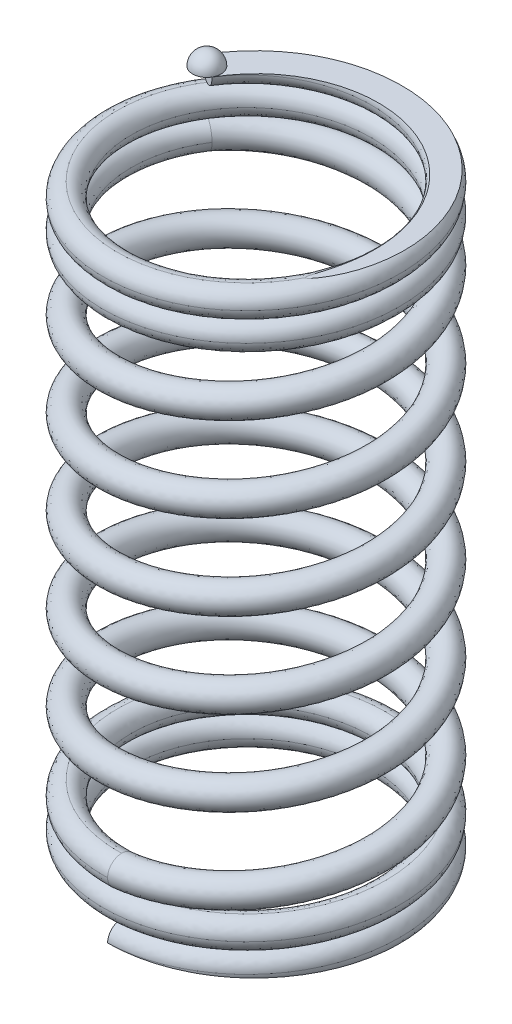
SolidWorks part; units mm, degrees
ref_plane "Front Plane" through (0, 0, 0) normal (0, 0, 1) x (1, 0, 0)
ref_plane "Top Plane" through (0, 0, 0) normal (0, 1, 0) x (1, 0, 0)
ref_plane "Right Plane" through (0, 0, 0) normal (1, 0, 0) x (0, 0, -1)
sketch "Sketch3" plane through (0, 0, 0) normal (0, 1, 0) x (1, 0, 0)
  circle A0 centre (0, 0) radius 4.75
  dimension "D1" = 9.5
ref_plane "Plane1" through (0, 2, 0) normal (0, 1, 0) x (1, 0, 0)
sketch "Sketch4" plane through (0, 0, 0) normal (0, 1, 0) x (1, 0, 0)
  circle A0 centre (0, 0) radius 4.75
  dimension "D1" = 9.5
curve "Helix/Spiral3" pitch 1 height 2 turns 2
sketch "Sketch5" plane through (0, 2, 0) normal (0, 1, 0) x (1, 0, 0)
  circle A0 centre (0, 0) radius 4.75
  dimension "D1" = 9.5
sketch "Sketch7" plane through (0, 0, 0) normal (1, 0, 0) x (0, 0, -1)
  line L0 (5.6185, 0) -> (-5.6185, 0) construction
  circle A0 centre (-4.75, 0) radius 0.5
  dimension "D2" = 1
  dimension "D1" = 4.75
sweep "Sweep5" add profiles "Sketch7" path "Helix/Spiral3"
sketch "Sketch13" plane through (0, 2, 0) normal (0, 1, 0) x (1, 0, 0)
  circle A0 centre (0, 0) radius 4.75
  dimension "D1" = 9.5
curve "Helix/Spiral6" pitch 3 height 17 turns 5.6667
sketch "Sketch15" plane through (0, 0, 0) normal (1, 0, 0) x (0, 0, -1)
  line L0 (5.6185, 2) -> (-5.6185, 2) construction
  circle A0 centre (-4.75, 2) radius 0.5
  spline S0 degree 3 poles (-4.75, 2) (-4.75, 2.0626) (-4.499, 2.1891) (-3.4274, 2.3777) (-1.8264, 2.5667) (0.0567, 2.7556) (1.9311, 2.9444) (3.5072, 3.1333) (4.5415, 3.3222) (4.8742, 3.5111) (4.454, 3.7) (3.3458, 3.8889) (1.7207, 4.0778) (-0.1702, 4.2667) (-2.0347, 4.4556) (-3.585, 4.6444) (-4.5815, 4.8333) (-4.8702, 5.0222) (-4.4067, 5.2111) (-3.2624, 5.4) (-1.6141, 5.5889) (0.2835, 5.7778) (2.1373, 5.9667) (3.6609, 6.1556) (4.6191, 6.3444) (4.8636, 6.5333) (4.3569, 6.7222) (3.1772, 6.9111) (1.5066, 7.1) (-0.3967, 7.2889) (-2.2387, 7.4778) (-3.7349, 7.6667) (-4.6541, 7.8556) (-4.8544, 8.0444) (-4.3048, 8.2333) (-3.0903, 8.4222) (-1.3983, 8.6111) (0.5096, 8.8) (2.3389, 8.9889) (3.8068, 9.1778) (4.6867, 9.3667) (4.8426, 9.5556) (4.2504, 9.7444) (3.0017, 9.9333) (1.2893, 10.1222) (-0.6223, 10.3111) (-2.4378, 10.5) (-3.8766, 10.6889) (-4.7167, 10.8778) (-4.8281, 11.0667) (-4.1937, 11.2556) (-2.9115, 11.4444) (-1.1795, 11.6333) (0.7347, 11.8222) (2.5354, 12.0111) (3.9444, 12.2) (4.7441, 12.3889) (4.811, 12.5778) (4.1347, 12.7667) (2.8197, 12.9556) (1.0691, 13.1444) (-0.8466, 13.3333) (-2.6316, 13.5222) (-4.01, 13.7111) (-4.769, 13.9) (-4.7913, 14.0889) (-4.0734, 14.2778) (-2.7264, 14.4667) (-0.9581, 14.6556) (0.9581, 14.8444) (2.7264, 15.0333) (4.0734, 15.2222) (4.7913, 15.4111) (4.769, 15.6) (4.01, 15.7889) (2.6316, 15.9778) (0.8466, 16.1667) (-1.0691, 16.3556) (-2.8197, 16.5444) (-4.1347, 16.7333) (-4.811, 16.9222) (-4.7441, 17.1111) (-3.9444, 17.3) (-2.5354, 17.4889) (-0.7347, 17.6778) (1.1795, 17.8667) (2.9115, 18.0556) (4.1936, 18.2444) (4.8282, 18.4333) (4.7162, 18.6223) (3.8782, 18.8109) (2.914, 18.9374) (2.375, 19) knots 0 0 0 0 0.011111 0.022222 0.033333 0.044444 0.055556 0.066667 0.077778 0.088889 0.1 0.111111 0.122222 0.133333 0.144444 0.155556 0.166667 0.177778 0.188889 0.2 0.211111 0.222222 0.233333 0.244444 0.255556 0.266667 0.277778 0.288889 0.3 0.311111 0.322222 0.333333 0.344444 0.355556 0.366667 0.377778 0.388889 0.4 0.411111 0.422222 0.433333 0.444444 0.455556 0.466667 0.477778 0.488889 0.5 0.511111 0.522222 0.533333 0.544444 0.555556 0.566667 0.577778 0.588889 0.6 0.611111 0.622222 0.633333 0.644444 0.655556 0.666667 0.677778 0.688889 0.7 0.711111 0.722222 0.733333 0.744444 0.755556 0.766667 0.777778 0.788889 0.8 0.811111 0.822222 0.833333 0.844444 0.855556 0.866667 0.877778 0.888889 0.9 0.911111 0.922222 0.933333 0.944444 0.955556 0.966667 0.977778 0.988889 1 1 1 1 construction
sweep "Sweep6" add profiles "Sketch15" path "Helix/Spiral6"
ref_plane "Plane4" through (0, 19, 0) normal (0, 1, 0) x (1, 0, 0)
sketch "Sketch16" plane through (0, 19, 0) normal (0, 1, 0) x (1, 0, 0)
  circle A0 centre (0, 0) radius 4.75
  dimension "D1" = 9.5
curve "Helix/Spiral7" pitch 1 height 2 turns 2
sketch "Sketch18" plane through (0, 0, 0) normal (-1, 0, 0) x (0, 0, 1)
  line L0 (5.6185, 0) -> (-5.6185, 0) construction
  line L1 (6.9903, 0) -> (-6.0243, 0)
  line L2 (6.9903, 0) -> (6.9903, -2.7149)
  line L3 (6.9903, -2.7149) -> (-6.0243, -2.7149)
  line L4 (-6.0243, 0) -> (-6.0243, -2.7149)
extrude "Cut-Extrude1" cut sketch "Sketch18" against normal mid plane 15
sketch "Sketch26" plane through (0, 19, 0) normal (0, 1, 0) x (1, 0, 0)
  circle A0 centre (0, 0) radius 4.75
  dimension "D1" = 9.5
curve "Helix/Spiral8" pitch 1 height 2 turns 2
sketch "Sketch27" plane through (0, 0, 0) normal (-0.5, 0, 0.866) x (0.866, 0, 0.5)
  circle A0 centre (-4.75, 19.0007) radius 0.5
sweep "Sweep7" add profiles "Sketch27" path "Helix/Spiral8"
sketch "Sketch28" plane through (0, 0, 0) normal (-0.5, 0, 0.866) x (0.866, 0, 0.5)
  line L0 (-5.3532, 21.0007) -> (-3.9959, 21.0007)
  line L1 (-3.9959, 21.0007) -> (7.3096, 21.0007)
  line L2 (7.3096, 21.0007) -> (7.3096, 23.8406)
  line L3 (7.3096, 23.8406) -> (-5.3532, 23.8406)
  line L4 (-5.3532, 23.8406) -> (-5.3532, 21.0007)
extrude "Cut-Extrude2" cut sketch "Sketch28" against normal mid plane 15
sketch "Sketch29" plane through (0, 0, 0) normal (-0.5, 0, 0.866) x (0.866, 0, 0.5)
  line L0 (-4.75, 21.7557) -> (-4.75, 19.8257) construction
  line L1 (-5.25, 21.0007) -> (-4.25, 21.0007) construction
  line L2 (-5.25, 21.0007) -> (-4.75, 21.0007)
  line L3 (-4.75, 21.0007) -> (-4.75, 21.5007)
  arc A0 (-4.75, 21.5007) -> (-5.25, 21.0007) centre (-4.75, 21.0007) ccw
revolve "Revolve1" add sketch "Sketch29" angle 360 about L0
sketch "Sketch30" plane through (0, 0, 0) normal (0, 0, 1) x (1, 0, 0)
  line L0 (0, 29.6261) -> (0, -9.9494) construction
sketch "Sketch31" plane through (0, 0, 0) normal (0, 0, 1) x (1, 0, 0)
  line L0 (0, 28.0718) -> (0, -6.2816) construction
